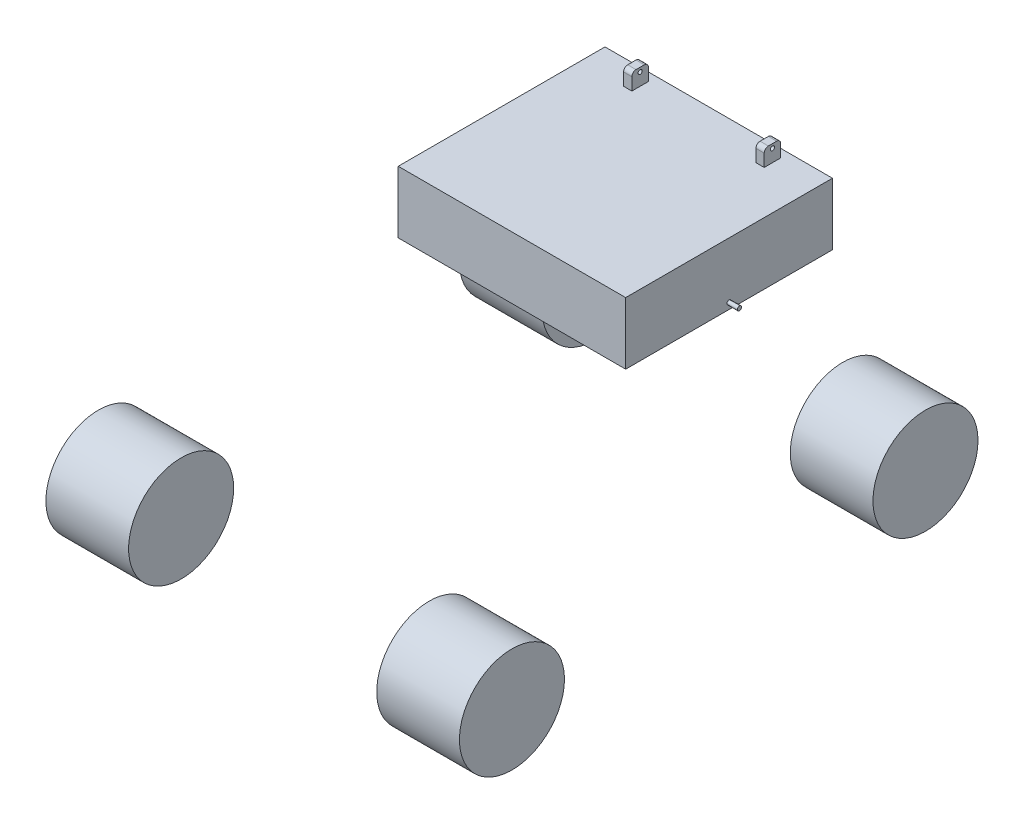
SolidWorks part; units mm, degrees
ref_plane "Front Plane" through (0, 0, 0) normal (0, 0, 1) x (1, 0, 0)
ref_plane "Top Plane" through (0, 0, 0) normal (0, 1, 0) x (1, 0, 0)
ref_plane "Right Plane" through (0, 0, 0) normal (1, 0, 0) x (0, 0, -1)
ref_plane "Plane1" through (300, 0, 0) normal (1, 0, 0) x (0, 0, -1)
sketch "Sketch2" plane through (300, 0, 0) normal (1, 0, 0) x (0, 0, -1)
  line L0 (-500, 0) -> (500, 0) construction
  circle A0 centre (-500, 0) radius 127
  circle A1 centre (500, 0) radius 127
  dimension "D1" = 254
  dimension "D2" = 1000
extrude "Boss-Extrude1" add sketch "Sketch2" along normal blind 200
mirror "Mirror4" about plane through (0, 0, 0) normal (1, 0, 0) of bodies 101 102
sketch "Sketch3" plane through (0, 0, 0) normal (1, 0, 0) x (0, 0, -1)
  line L1 (0, 500) -> (500, 500)
  line L2 (0, 500) -> (0, 350)
  line L3 (0, 350) -> (500, 350)
  line L4 (500, 500) -> (500, 350)
  dimension "D1" = 500
  dimension "D2" = 150
  dimension "D3" = 350
extrude "Boss-Extrude2" add sketch "Sketch3" along normal mid plane 550 separate body
sketch "Sketch4" plane through (275, 0, 0) normal (1, 0, 0) x (0, 0, -1)
  line L0 (0, 350) -> (500, 350) construction
  line L1 (250, 500) -> (250, 365) construction
  line L2 (500, 500) -> (0, 500) construction
  circle A0 centre (250, 365) radius 5
  dimension "D1" = 15
  dimension "D2" = 10
extrude "Boss-Extrude3" add sketch "Sketch4" along normal up to surface (25 mm away) up to face at (300, 0, -627)
mirror "Mirror6" about plane through (0, 0, 0) normal (1, 0, 0) of "Boss-Extrude3"
sketch "Sketch5" plane through (0, 500, 0) normal (0, 1, 0) x (1, 0, 0)
  line L0 (-215, 490) -> (215, 490)
  line L1 (-210, 485) -> (210, 485)
  line L2 (-210, 485) -> (-210, 245)
  line L3 (-210, 245) -> (210, 245)
  line L4 (210, 485) -> (210, 245)
  line L5 (215, 490) -> (215, 240)
  line L6 (-215, 240) -> (215, 240)
  line L7 (-215, 490) -> (-215, 240)
  line L8 (0, 0) -> (0, 240) construction
  dimension "D1" = 5
  dimension "D2" = 240
  dimension "D3" = 430
  dimension "D4" = 250
sketch "Sketch6" plane through (0, 500, 0) normal (0, 1, 0) x (1, 0, 0)
  line L0 (-150, 460) -> (150, 460) construction
  line L1 (-170, 440) -> (-150, 440)
  line L2 (-170, 440) -> (-170, 480)
  line L3 (-170, 480) -> (-150, 480)
  line L4 (-150, 440) -> (-150, 480)
  line L5 (150, 440) -> (170, 440)
  line L6 (150, 440) -> (150, 480)
  line L7 (150, 480) -> (170, 480)
  line L8 (170, 440) -> (170, 480)
  line L9 (0, 0) -> (0, 460) construction
  dimension "D1" = 300
  dimension "D2" = 40
  dimension "D3" = 20
  dimension "D4" = 460
extrude "Boss-Extrude4" add sketch "Sketch6" along normal blind 40
fillet "Fillet1" radius 10 4 edges at (160, 540, -440) (160, 540, -480) (-160, 540, -440) (-160, 540, -480)
sketch "Sketch7" plane through (170, 0, 0) normal (1, 0, 0) x (0, 0, -1)
  line L0 (460, 540) -> (460, 530) construction
  line L1 (450, 540) -> (470, 540) construction
  circle A0 centre (460, 530) radius 5
  dimension "D1" = 10
  dimension "D2" = 10
extrude "Cut-Extrude1" cut sketch "Sketch7" against normal through all
sketch "Sketch8" plane through (0, 0, 0) normal (1, 0, 0) x (0, 0, -1)
  line L0 (-130, 350) -> (-891.8102, -49.5089)
  line L1 (170, 550) -> (170, 1010) construction
  line L2 (379.7754, 881.1254) -> (375.0079, 531.1578) construction
  line L3 (170, 1010) -> (-891.8102, -49.5089)
  line L4 (170, 1010) -> (-891.8102, -49.5089) construction
  line L5 (219.4437, 960.4489) -> (-842.3665, -99.06) construction
  line L6 (120.5563, 1059.5511) -> (-941.254, 0.0423) construction
  line L7 (0, 0) -> (500, 0) construction
  line L8 (460, 530) -> (290.0158, 532.3157)
  line L9 (-519.0609, -125.5615) -> (-1143.494, -125.5615) construction
  line L10 (500, 500) -> (0, 500) construction
  line L11 (0, 500) -> (0, 350) construction
  line L12 (179.794, 883.8497) -> (290.0158, 532.3157)
  line L14 (460, 530) -> (579.7569, 878.401)
  line L15 (579.7569, 878.401) -> (179.794, 883.8497)
  circle A0 centre (-130, 350) radius 860.2105 construction
  circle A1 centre (170, 550) radius 460 construction
  arc A2 (219.4437, 960.4489) -> (120.5563, 1059.5511) centre (170, 1010) ccw construction
  arc A3 (-941.254, 0.0423) -> (-842.3665, -99.06) centre (-891.8102, -49.5089) ccw construction
  circle A4 centre (-500, 0) radius 127 construction
  point P6 (-360.9051, 480.2456)
  point P11 (0, 350)
  point P37 (375.0079, 531.1578)
  dimension "D1" = 70
  dimension "D4" = 1500
  dimension "D2" = 170
  dimension "D3" = 130
  dimension "D6" = 50
  dimension "D7" = 170
  dimension "D8" = 460
  dimension "D9" = 400
  dimension "D10" = 350
